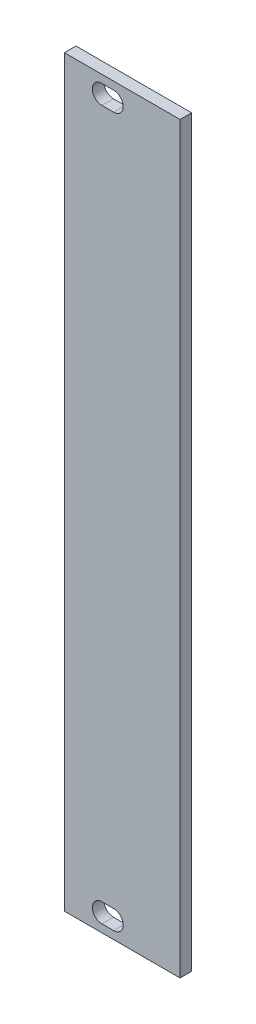
SolidWorks part; units mm, degrees
ref_plane "Front Plane" through (0, 0, 0) normal (0, 0, 1) x (1, 0, 0)
ref_plane "Top Plane" through (0, 0, 0) normal (0, 1, 0) x (1, 0, 0)
ref_plane "Right Plane" through (0, 0, 0) normal (1, 0, 0) x (0, 0, -1)
sketch "Sketch1" plane through (0, 0, 0) normal (0, 0, 1) x (1, 0, 0)
  line L0 (-2.5, 64.25) -> (-2.5, -64.25) construction
  line L1 (-10, 64.25) -> (10, 64.25)
  line L2 (-10, 64.25) -> (-10, -64.25)
  line L3 (-10, -64.25) -> (10, -64.25)
  line L4 (10, 64.25) -> (10, -64.25)
  line L5 (-10, 64.25) -> (10, -64.25) construction
  line L6 (-10, -64.25) -> (10, 64.25) construction
  line L7 (-10, 61.25) -> (10, 61.25) construction
  line L8 (-10, -61.25) -> (10, -61.25) construction
  line L9 (-3.516, -61.25) -> (-1.484, -61.25) construction
  line L11 (-3.516, -59.6) -> (-1.484, -59.6)
  line L12 (-3.516, -62.9) -> (-1.484, -62.9)
  line L13 (-3.516, 61.25) -> (-1.484, 61.25) construction
  line L14 (-3.516, 62.9) -> (-1.484, 62.9)
  line L15 (-3.516, 59.6) -> (-1.484, 59.6)
  arc A0 (-3.516, -59.6) -> (-3.516, -62.9) centre (-3.516, -61.25) ccw
  arc A1 (-1.484, -62.9) -> (-1.484, -59.6) centre (-1.484, -61.25) ccw
  arc A2 (-3.516, 62.9) -> (-3.516, 59.6) centre (-3.516, 61.25) ccw
  arc A3 (-1.484, 59.6) -> (-1.484, 62.9) centre (-1.484, 61.25) ccw
  point P0 (0, 0)
  point P18 (-2.5, -61.25)
  point P24 (-2.5, 61.25)
  dimension "D6" = 1.65
  dimension "D7" = 1.65
  dimension "D1" = 128.5
  dimension "D2" = 20
  dimension "D3" = 7.5
  dimension "D4" = 3
  dimension "D8" = 2.032
  dimension "D9" = 2.032
  dimension "D5" = 3
extrude "Boss-Extrude1" add sketch "Sketch1" along normal blind 2
